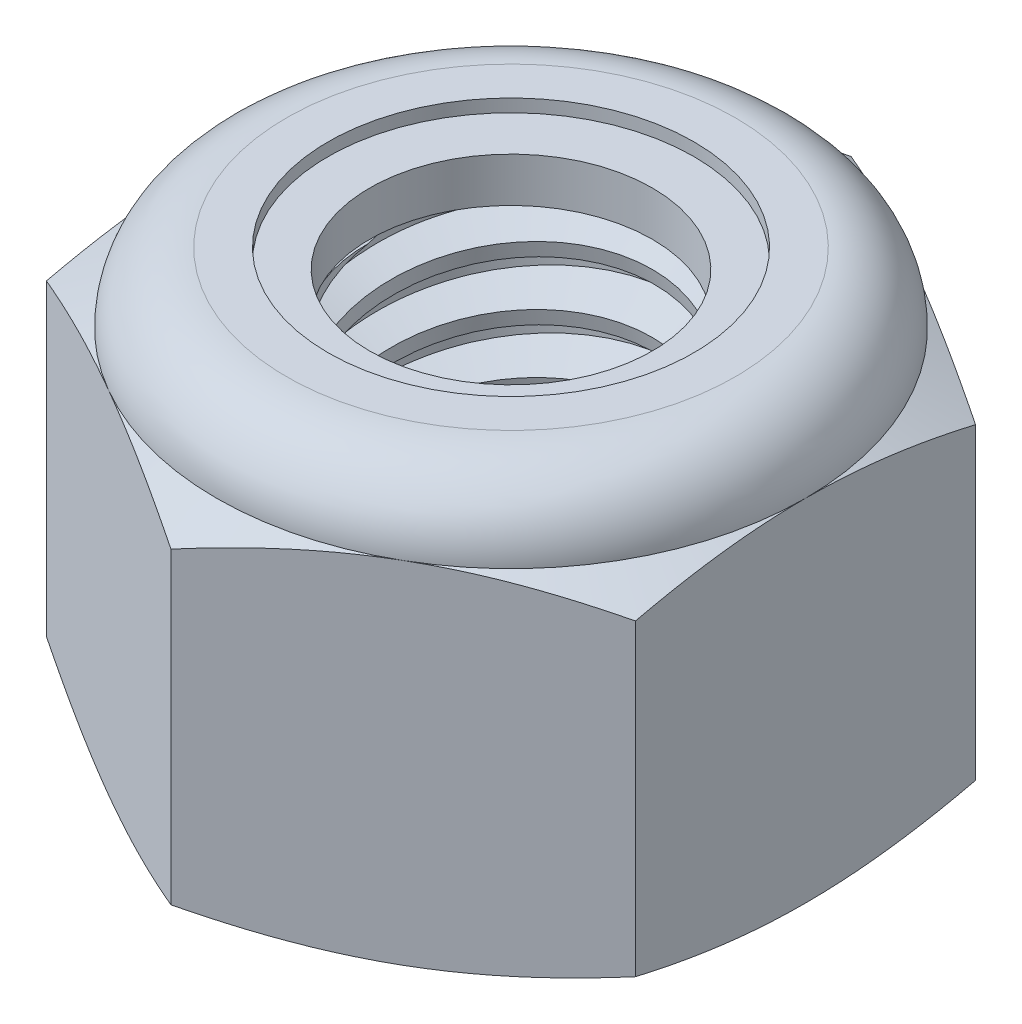
SolidWorks part; units mm, degrees
material "AISI 316 Annealed Stainless Steel Bar (SS)"
ref_plane "Front" through (0, 0, 0) normal (0, 0, 1) x (1, 0, 0)
ref_plane "Top" through (0, 0, 0) normal (0, 1, 0) x (1, 0, 0)
ref_plane "Right" through (0, 0, 0) normal (1, 0, 0) x (0, 0, -1)
sketch "Sketch1" plane through (0, 0, 0) normal (0, 1, 0) x (1, 0, 0)
  line L1 (0, 4.0415) -> (-3.5, 2.0207)
  line L2 (-3.5, 2.0207) -> (-3.5, -2.0207)
  line L3 (-3.5, -2.0207) -> (0, -4.0415)
  line L4 (0, -4.0415) -> (3.5, -2.0207)
  line L5 (3.5, -2.0207) -> (3.5, 2.0207)
  line L6 (3.5, 2.0207) -> (0, 4.0415)
  circle A0 centre (0, 0) radius 3.5 construction
  dimension "Hex Flats" = 7
extrude "Extrude1" add sketch "Sketch1" along normal blind 5
sketch "Sketch2" plane through (0, 0, 0) normal (1, 0, 0) x (0, 0, -1)
  line L0 (-2, 0) -> (-2, 5) construction
  line L1 (0, 0) -> (2, 0)
  line L2 (0, 0) -> (0, 5)
  line L3 (0, 5) -> (2, 5)
  line L4 (2, 0) -> (2, 5)
  line L5 (-2.0207, 5) -> (2.0207, 5) construction
  line L7 (0, -2) -> (0, 0) construction
  dimension "Thread Dia" = 4
revolve "Revolve1" add sketch "Sketch2" angle 360 about L7
sketch "Sketch3" plane through (0, 0, 0) normal (1, 0, 0) x (0, 0, -1)
  line L0 (2, 5) -> (-2, 5) construction
  line L1 (-2, 5) -> (-2, 4.3) construction
  line L2 (-2, 4.3) -> (2, 5) construction
  line L3 (2, 5) -> (2.0151, 4.9138) construction
  line L4 (2.0151, 4.9138) -> (2.1207, 4.3105)
  line L5 (2.1207, 4.3105) -> (1.7097, 4.4606)
  line L6 (1.7097, 4.4606) -> (1.6796, 4.633)
  line L7 (1.6796, 4.633) -> (2.0151, 4.9138)
  line L8 (1.6947, 4.5468) -> (2.0679, 4.6121) construction
  line L9 (2, 5) -> (2, 4.6003) construction
  line L10 (2, 4.6003) -> (-2, 3.9003) construction
  line L11 (-2, 3.9003) -> (-2, 4.3) construction
  line L12 (-0.1312, 5) -> (0.1312, 3.5005) construction
  line L13 (-2, 0) -> (-2, 5) construction
  line L14 (0, 5) -> (2, 5) construction
  line L15 (2, 0) -> (2, 5) construction
  point P13 (0, 4.2503)
  dimension "D1" = 0.0875
  dimension "D2" = 0.175
  dimension "Thread Pitch" = 0.7
  dimension "D4" = 60
  dimension "D5" = 0.7
revolve "Cut-Revolve1" cut sketch "Sketch3" angle 360 about L12
pattern_linear "LPattern1" count 7 spacing 0.7 along (0, -1, 0) count 2 spacing 0.7 along (0, 1, 0) of "Cut-Revolve1"
sketch "Sketch4" plane through (0, 0, 0) normal (1, 0, 0) x (0, 0, -1)
  line L0 (0, 5) -> (2, 5)
  line L1 (2, 5) -> (1.6796, 4.8506)
  line L2 (1.6796, 4.8506) -> (1.6796, 0.1494)
  line L3 (1.6796, 0.1494) -> (2, 0)
  line L4 (2, 0) -> (0, 0)
  line L5 (0, 0) -> (0, 5)
  line L6 (2, 0) -> (2, 5) construction
  line L7 (0, 5) -> (2, 5) construction
  line L8 (0, 0) -> (2, 0) construction
  line L9 (0, 0) -> (0, 5) construction
  line L10 (0, 5) -> (0, 5.3535) construction
  dimension "D1" = 25
revolve "Cut-Revolve2" cut sketch "Sketch4" angle 360 about L10
combine bodies "Combine1" operation type subtract main body 112
sketch "Sketch5" plane through (0, 0, 0) normal (1, 0, 0) x (0, 0, -1)
  line L0 (0, 0) -> (3.5, 0)
  line L1 (3.5, 0) -> (4.0415, 0.2525)
  line L2 (4.0415, 0.2525) -> (4.0415, 3.9142)
  line L3 (4.0415, 3.9142) -> (3.5, 4.1667)
  line L4 (2.6667, 5) -> (2.6667, 6.27)
  line L5 (2.6667, 6.27) -> (5.3115, 6.27)
  line L6 (5.3115, 6.27) -> (5.3115, -1.27)
  line L7 (5.3115, -1.27) -> (0, -1.27)
  line L8 (0, -1.27) -> (0, 0)
  line L9 (3.5, 4.1667) -> (3.5, 0) construction
  line L10 (0, 0) -> (2, 0) construction
  line L13 (4.0415, 2.0833) -> (5.3115, 2.0833) construction
  line L14 (4.0415, 5) -> (4.0415, 0) construction
  line L15 (0, 0) -> (0, 6.27) construction
  line L20 (0, 6.27) -> (2.6667, 6.27) construction
  line L22 (0, 5) -> (2, 5) construction
  arc A0 (3.5, 4.1667) -> (2.6667, 5) centre (2.6667, 4.1667) ccw
  dimension "D1" = 25
  dimension "D2" = 1.27
  dimension "D3" = 5
  dimension "D4" = 0.8333
revolve "Cut-Revolve3" cut sketch "Sketch5" angle 360 about L15
sketch "Sketch6" plane through (0, 0, 0) normal (1, 0, 0) x (0, 0, -1)
  line L0 (0, 4.1667) -> (3.3476, 4.1667)
  line L1 (2.6667, 4.8476) -> (2.1731, 4.8476)
  line L2 (0, 6.27) -> (0, 4.1667)
  line L3 (2.1731, 6.27) -> (0, 6.27)
  line L4 (0, 6.27) -> (2.6667, 6.27) construction
  line L5 (0, 0) -> (0, 6.27) construction
  line L6 (0, 6.27) -> (0, 44.323) construction
  line L7 (2.1731, 4.8476) -> (2.1731, 6.27)
  line L8 (2.6667, 5) -> (2.6667, 4.8476) construction
  line L9 (2.1731, 4.8476) -> (1.6796, 4.8476) construction
  line L10 (1.6796, 4.8476) -> (1.6796, 4.8506) construction
  arc A0 (3.3476, 4.1667) -> (2.6667, 4.8476) centre (2.6667, 4.1667) ccw
  arc A1 (3.5, 4.1667) -> (2.6667, 5) centre (2.6667, 4.1667) ccw construction
  dimension "D1" = 0.1524
revolve "Cut-Revolve4" cut sketch "Sketch6" angle 360 about L6
sketch "Sketch7" plane through (0, 0, 0) normal (1, 0, 0) x (0, 0, -1)
  line L0 (1.6796, 4.2429) -> (3.2666, 4.2429)
  line L1 (2.6667, 4.7714) -> (1.6796, 4.7714)
  line L2 (1.6796, 4.7714) -> (1.6796, 4.2429)
  line L3 (1.6796, 4.2429) -> (0, 4.2429) construction
  line L4 (0, 4.2429) -> (0, 4.7714) construction
  line L5 (0, 4.7714) -> (1.6796, 4.7714) construction
  line L6 (1.6796, 4.2429) -> (1.6796, 4.1667) construction
  line L7 (0, 4.1667) -> (3.3476, 4.1667) construction
  line L8 (2.6667, 4.7714) -> (2.6667, 4.8476) construction
  arc A0 (3.2666, 4.2429) -> (2.6667, 4.7714) centre (2.6667, 4.1667) ccw
  arc A2 (3.3476, 4.1667) -> (2.6667, 4.8476) centre (2.6667, 4.1667) ccw construction
  dimension "D1" = 0.0762
revolve "Revolve2" add sketch "Sketch7" angle 360 about L4
equation "\"D1@Sketch3\"=\"Thread Pitch@Sketch3\"/8"
equation "\"D2@Sketch3\"=\"Thread Pitch@Sketch3\"/4"
equation "\"D5@Sketch3\"=\"Thread Pitch@Sketch3\""
equation "\"D4@LPattern1\"=\"Thread Pitch@Sketch3\""
equation "\"D3@LPattern1\"=\"Thread Pitch@Sketch3\""
equation "\"D1@LPattern1\"=\"Height@Extrude1\"/\"Thread Pitch@Sketch3\""
equation "\"D4@Sketch5\"=\"Height@Extrude1\"/6"
